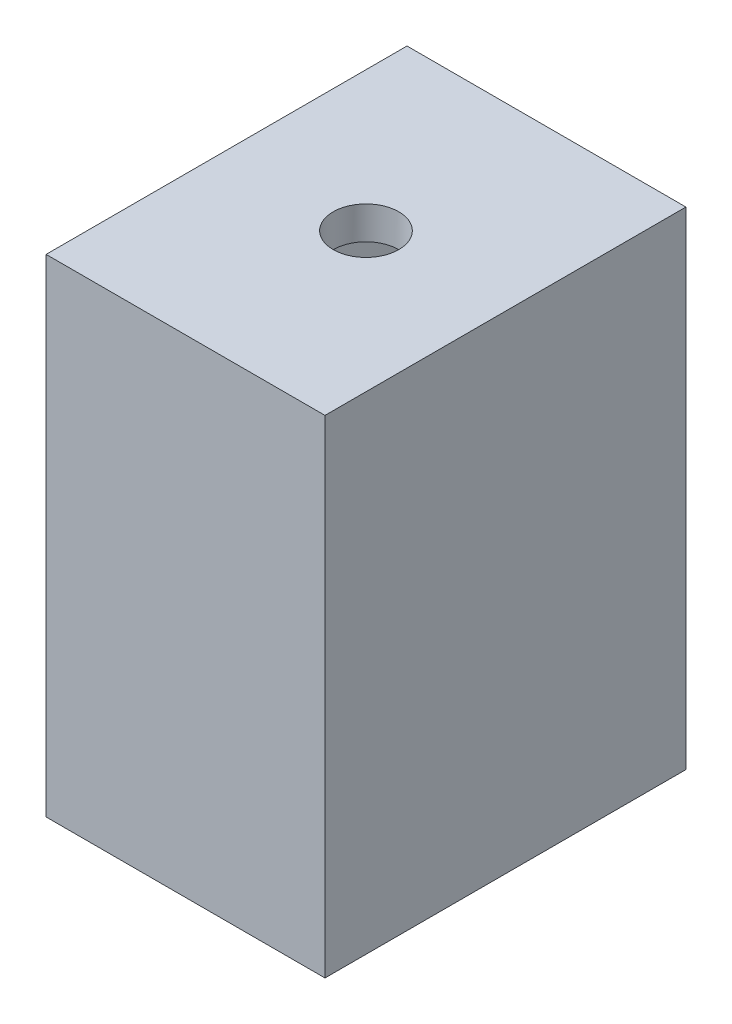
SolidWorks part; units mm, degrees
ref_plane "Front Plane" through (0, 0, 0) normal (0, 0, 1) x (1, 0, 0)
ref_plane "Top Plane" through (0, 0, 0) normal (0, 1, 0) x (1, 0, 0)
ref_plane "Right Plane" through (0, 0, 0) normal (1, 0, 0) x (0, 0, -1)
sketch "Sketch1" plane through (0, 0, 0) normal (0, 0, 1) x (1, 0, 0)
  line L1 (0, 0) -> (17, 0)
  line L2 (0, 0) -> (0, 29.7)
  line L3 (0, 29.7) -> (17, 29.7)
  line L4 (17, 0) -> (17, 29.7)
  dimension "D1" = 29.7
  dimension "D2" = 17
extrude "Boss-Extrude1" add sketch "Sketch1" along normal blind 22
sketch "Sketch2" plane through (0, 29.7, 0) normal (0, 1, 0) x (1, 0, 0)
  line L0 (17, -22) -> (0, 0) construction
  line L1 (0, -22) -> (17, 0) construction
  circle A0 centre (8.5, -11) radius 2
  point P10 (8.5, -11)
  dimension "D1" = 4
extrude "Cut-Extrude1" cut sketch "Sketch2" against normal through all
sketch "Sketch3" plane through (0, 0, 0) normal (0, -1, 0) x (1, 0, 0)
  circle A0 centre (8.5, 11) radius 4
  dimension "D1" = 8
extrude "Cut-Extrude2" cut sketch "Sketch3" against normal blind 27.7
sketch "Sketch4" plane through (0, 0, 0) normal (0, -1, 0) x (1, 0, 0)
  line L14 (15, 2) -> (15, 20)
  line L15 (15, 20) -> (2, 20)
  line L16 (2, 20) -> (2, 2)
  line L17 (2, 2) -> (15, 2)
  line L18 (15, 2) -> (15, 20)
  line L19 (15, 20) -> (2, 20)
  line L20 (2, 20) -> (2, 2)
  line L21 (2, 2) -> (15, 2)
  dimension "D1" = 2
extrude "Cut-Extrude4" cut sketch "Sketch4" against normal blind 25.7 from offset 2 offset against normal yes
